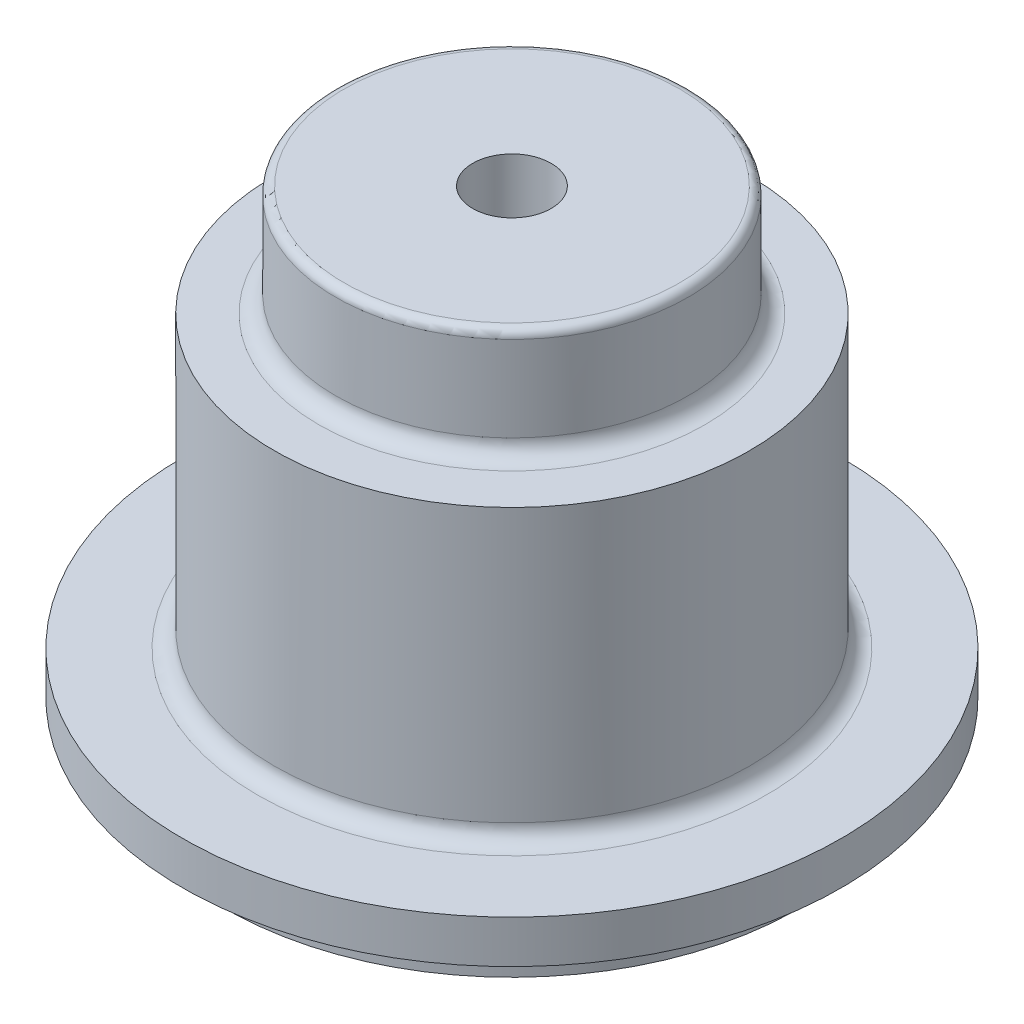
SolidWorks part; units mm, degrees
ref_plane "Front Plane" through (0, 0, 0) normal (0, 0, 1) x (1, 0, 0)
ref_plane "Top Plane" through (0, 0, 0) normal (0, 1, 0) x (1, 0, 0)
ref_plane "Right Plane" through (0, 0, 0) normal (1, 0, 0) x (0, 0, -1)
sketch "Sketch1" plane through (0, 0, 0) normal (0, 0, 1) x (1, 0, 0)
  line L0 (0, 0) -> (0, 49.2)
  line L1 (12.3346, 0) -> (21.75, 0)
  line L2 (21.75, 0) -> (21.75, 3)
  line L3 (21.75, 3) -> (25, 3)
  line L4 (25, 3) -> (25, 6.25)
  line L5 (25, 6.25) -> (18.0356, 6.25)
  line L6 (2.9747, 28.2359) -> (2.9747, 36.6111)
  line L9 (2.9747, 36.6111) -> (13.3704, 36.6111)
  line L10 (12.3346, 0) -> (12.3346, 25.3)
  line L11 (12.3346, 25.3) -> (2.9747, 25.3)
  line L12 (18.0356, 6.25) -> (18.0356, 28.2359)
  line L13 (18.0356, 28.2359) -> (13.3704, 28.2359)
  line L14 (13.3704, 28.2359) -> (13.3704, 36.6111)
  line L15 (2.9747, 28.2359) -> (0, 28.2359)
  line L16 (0, 28.2359) -> (0, 25.3)
  line L17 (0, 25.3) -> (2.8306, 25.3)
  line L18 (2.9747, 25.3) -> (2.8306, 25.3)
  dimension "D1" = 49.2
  dimension "D5" = 25.3
  dimension "D6" = 21.75
  dimension "D7" = 25
  dimension "D8" = 3
  dimension "D9" = 3.25
revolve "Revolve4" add sketch "Sketch1" angle 360 about L0
fillet "Fillet2" radius 1.27 2 edges at (0, 6.25, -18.0356) (0, 28.2359, -13.3704)
fillet "Fillet3" radius 0.635 1 edges at (0, 36.6111, -13.3704)
equation "\"`1mm\"=10"
